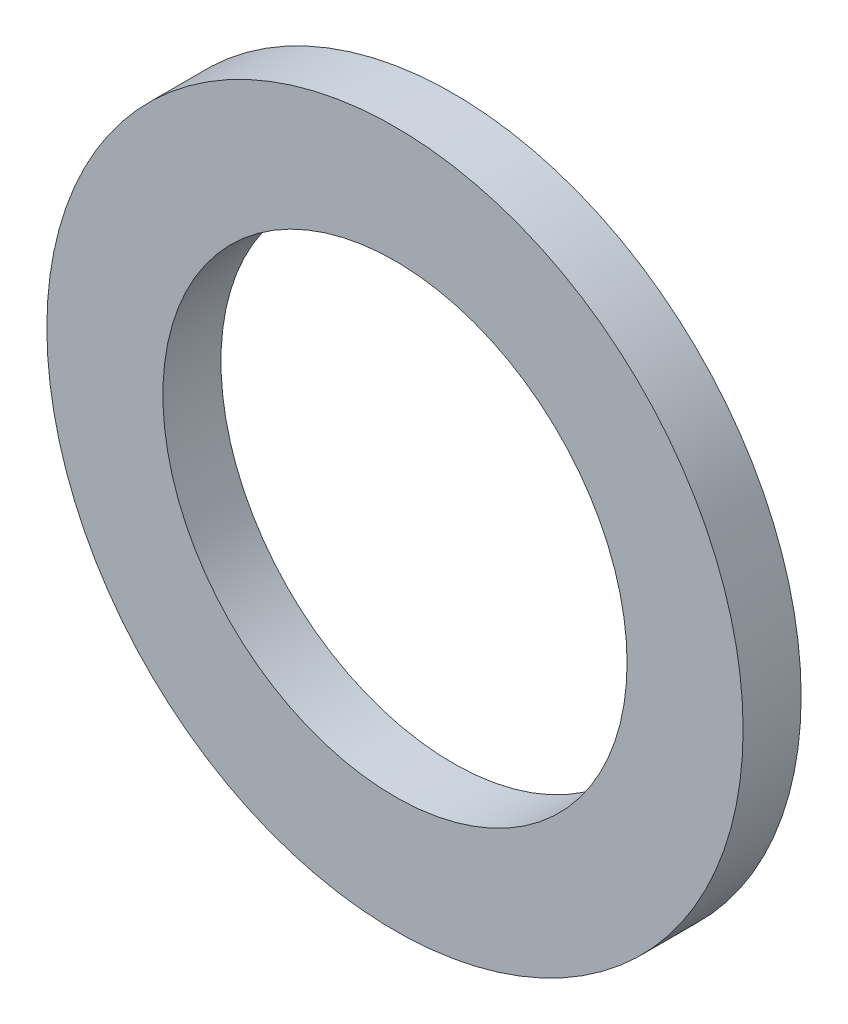
SolidWorks part; units mm, degrees
ref_plane "Front Plane" through (0, 0, 0) normal (0, 0, 1) x (1, 0, 0)
ref_plane "Top Plane" through (0, 0, 0) normal (0, 1, 0) x (1, 0, 0)
ref_plane "Right Plane" through (0, 0, 0) normal (1, 0, 0) x (0, 0, -1)
sketch "Sketch1" plane through (0, 0, 0) normal (0, 0, 1) x (1, 0, 0)
  circle A0 centre (0, 0) radius 6.35
  circle A1 centre (0, 0) radius 9.525
  dimension "D2" = 12.7
  dimension "D1" = 3.175
extrude "Boss-Extrude1" add sketch "Sketch1" along normal blind 1.5875
